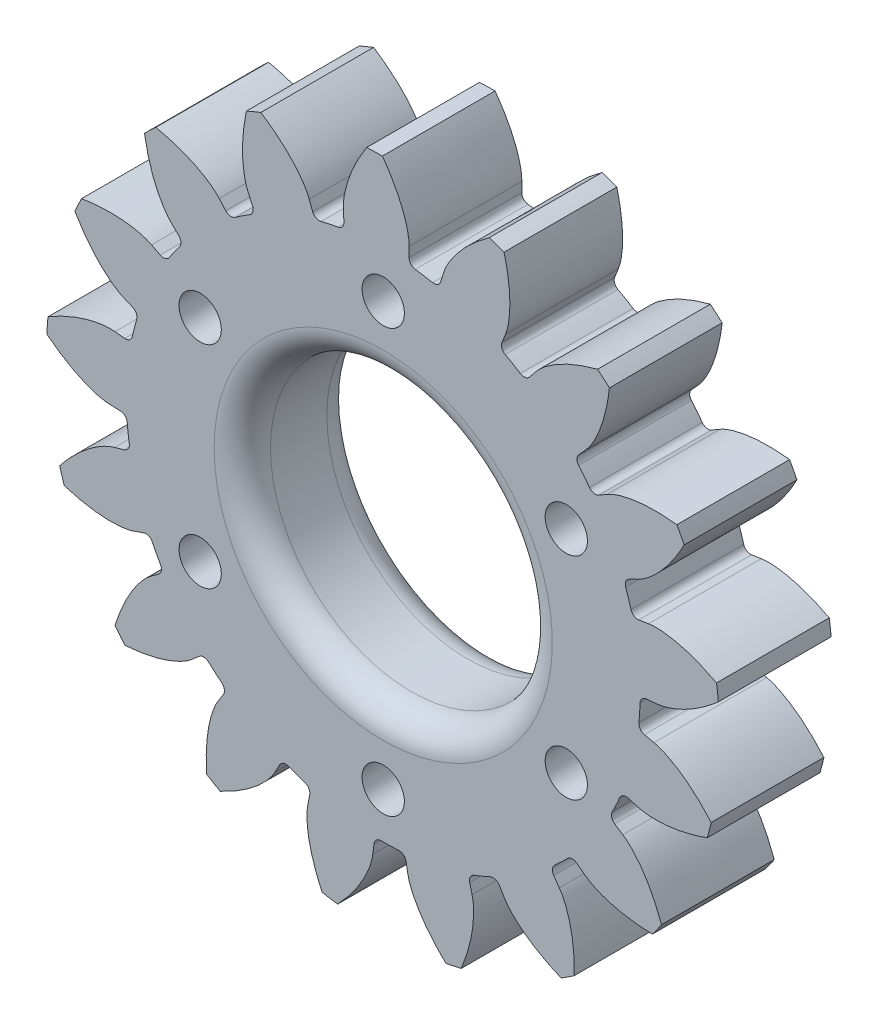
SolidWorks part; units mm, degrees
ref_plane "Front" through (0, 0, 0) normal (0, 0, 1) x (1, 0, 0)
ref_plane "Top" through (0, 0, 0) normal (0, 1, 0) x (1, 0, 0)
ref_plane "Right" through (0, 0, 0) normal (1, 0, 0) x (0, 0, -1)
sketch "Sketch1" plane through (0, 0, 0) normal (0, 0, 1) x (1, 0, 0)
  line L68 (2.1427, 9.4464) -> (2.0368, 9.1165)
  line L69 (0.916, 9.2963) -> (0.9185, 9.6427)
  line L70 (-1.4144, 9.5825) -> (-1.394, 9.2367)
  line L71 (-2.504, 8.9994) -> (-2.6268, 9.3234)
  line L72 (-4.7805, 8.4245) -> (-4.6366, 8.1093)
  line L73 (-5.5859, 7.4871) -> (-5.8174, 7.7449)
  line L74 (-7.501, 6.1287) -> (-7.2529, 5.8868)
  line L75 (-7.9134, 4.9637) -> (-8.2224, 5.1204)
  line L76 (-9.2084, 3.0052) -> (-8.8897, 2.8692)
  line L77 (-9.1721, 1.7699) -> (-9.5168, 1.8043)
  line L78 (-9.6722, -0.5242) -> (-9.3259, -0.5358)
  line L79 (-9.1921, -1.663) -> (-9.526, -1.7554)
  line L80 (-8.8296, -3.9828) -> (-8.5026, -3.8686)
  line L81 (-7.9706, -4.8713) -> (-8.2486, -5.078)
  line L82 (-6.7946, -6.9035) -> (-6.5309, -6.6788)
  line L83 (-5.6727, -7.4216) -> (-5.8572, -7.7148)
  line L84 (-3.842, -8.8918) -> (-3.6772, -8.587)
  line L85 (-2.6086, -8.9696) -> (-2.6747, -9.3097)
  line L86 (-0.3704, -9.6793) -> (-0.3269, -9.3356)
  line L87 (0.8078, -9.3063) -> (0.8689, -9.6473)
  line L88 (3.1511, -9.1595) -> (3.0675, -8.8232)
  line L89 (4.115, -8.3861) -> (4.2953, -8.6819)
  line L90 (6.2471, -7.4026) -> (6.0477, -7.1193)
  line L91 (6.8665, -6.3332) -> (7.1415, -6.544)
  line L92 (8.4994, -4.646) -> (8.2111, -4.4539)
  line L93 (8.6907, -3.4251) -> (9.0232, -3.5223)
  line L94 (9.6038, -1.2619) -> (9.2656, -1.1869)
  line L95 (9.3411, -0.0544) -> (9.6863, -0.0249)
  line L96 (9.4111, 2.2926) -> (9.0686, 2.2404)
  line L97 (8.73, 3.3237) -> (9.0412, 3.4759)
  line L98 (7.9475, 5.5374) -> (7.6469, 5.365)
  line L99 (6.9398, 6.2529) -> (7.1751, 6.5072)
  line L100 (5.4104, 8.0345) -> (5.1925, 7.7651)
  line L101 (4.2123, 8.3376) -> (4.3399, 8.6597)
  circle A0 centre (0, 0) radius 5
  arc A136 (4.2867, 11.1494) -> (3.764, 11.3366) centre (0, 0) ccw
  arc A137 (1.7491, 8.9466) -> (2.0368, 9.1165) centre (1.7973, 9.1934) ccw
  arc A138 (1.7491, 8.9466) -> (1.1361, 9.0449) centre (0, 0) ccw
  arc A139 (0.916, 9.2963) -> (1.1361, 9.0449) centre (1.1675, 9.2944) ccw
  arc A140 (-0.0304, 11.945) -> (-0.5854, 11.9307) centre (0, 0) ccw
  arc A141 (-1.6009, 8.9743) -> (-1.394, 9.2367) centre (-1.6451, 9.2219) ccw
  arc A142 (-1.6009, 8.9743) -> (-2.208, 8.8445) centre (0, 0) ccw
  arc A143 (-2.504, 8.9994) -> (-2.208, 8.8445) centre (-2.2689, 9.0885) ccw
  arc A144 (-4.3434, 11.1274) -> (-4.8558, 10.9136) centre (0, 0) ccw
  arc A145 (-4.7347, 7.79) -> (-4.6366, 8.1093) centre (-4.8653, 8.0049) ccw
  arc A146 (-4.7347, 7.79) -> (-5.2539, 7.4497) centre (0, 0) ccw
  arc A147 (-5.5859, 7.4871) -> (-5.2539, 7.4497) centre (-5.3988, 7.6552) ccw
  arc A148 (-8.0698, 8.807) -> (-8.4703, 8.4225) centre (0, 0) ccw
  arc A149 (-7.229, 5.5536) -> (-7.2529, 5.8868) centre (-7.4285, 5.7068) ccw
  arc A150 (-7.229, 5.5536) -> (-7.5902, 5.0487) centre (0, 0) ccw
  arc A151 (-7.9134, 4.9637) -> (-7.5902, 5.0487) centre (-7.7996, 5.188) ccw
  arc A152 (-10.7063, 5.2971) -> (-10.9409, 4.7939) centre (0, 0) ccw
  arc A153 (-8.7471, 2.5671) -> (-8.8897, 2.8692) centre (-8.9884, 2.6379) ccw
  arc A154 (-8.7471, 2.5671) -> (-8.9015, 1.9659) centre (0, 0) ccw
  arc A155 (-9.1721, 1.7699) -> (-8.9015, 1.9659) centre (-9.147, 2.0201) ccw
  arc A156 (-11.8969, 1.0719) -> (-11.9338, 0.5179) centre (0, 0) ccw
  arc A157 (-9.0837, -0.766) -> (-9.3259, -0.5358) centre (-9.3343, -0.7872) ccw
  arc A158 (-9.0837, -0.766) -> (-9.0105, -1.3825) centre (0, 0) ccw
  arc A159 (-9.1921, -1.663) -> (-9.0105, -1.3825) centre (-9.2591, -1.4206) ccw
  arc A160 (-11.4807, -3.2982) -> (-11.3151, -3.8281) centre (0, 0) ccw
  arc A161 (-8.1936, -3.9957) -> (-8.5026, -3.8686) centre (-8.4196, -4.106) ccw
  arc A162 (-8.1936, -3.9957) -> (-7.9027, -4.5441) centre (0, 0) ccw
  arc A163 (-7.9706, -4.8713) -> (-7.9027, -4.5441) centre (-8.1207, -4.6695) ccw
  arc A164 (-9.514, -7.2228) -> (-9.1681, -7.6571) centre (0, 0) ccw
  arc A165 (-6.1969, -6.6858) -> (-6.5309, -6.6788) centre (-6.3678, -6.8702) ccw
  arc A166 (-6.1969, -6.6858) -> (-5.7275, -7.092) centre (0, 0) ccw
  arc A167 (-5.6727, -7.4216) -> (-5.7275, -7.092) centre (-5.8855, -7.2877) ccw
  arc A168 (-6.2624, -10.1719) -> (-5.783, -10.4519) centre (0, 0) ccw
  arc A169 (-3.3632, -8.4729) -> (-3.6772, -8.587) centre (-3.456, -8.7066) ccw
  arc A170 (-3.3632, -8.4729) -> (-2.7788, -8.6821) centre (0, 0) ccw
  arc A171 (-2.6086, -8.9696) -> (-2.7788, -8.6821) centre (-2.8554, -8.9216) ccw
  arc A172 (-2.165, -11.7472) -> (-1.6168, -11.8352) centre (0, 0) ccw
  arc A173 (-0.0754, -9.1157) -> (-0.3269, -9.3356) centre (-0.0774, -9.3671) ccw
  arc A174 (-0.0754, -9.1157) -> (0.5452, -9.0997) centre (0, 0) ccw
  arc A175 (0.8078, -9.3063) -> (0.5452, -9.0997) centre (0.5602, -9.3507) ccw
  arc A176 (2.2248, -11.7361) -> (2.7677, -11.62) centre (0, 0) ccw
  arc A177 (3.2227, -8.5273) -> (3.0675, -8.8232) centre (3.3116, -8.7626) ccw
  arc A178 (3.2227, -8.5273) -> (3.7956, -8.2882) centre (0, 0) ccw
  arc A179 (4.115, -8.3861) -> (3.7956, -8.2882) centre (3.9003, -8.5169) ccw
  arc A180 (6.3141, -10.1399) -> (6.7785, -9.8355) centre (0, 0) ccw
  arc A181 (6.0855, -6.7873) -> (6.0477, -7.1193) centre (6.2534, -6.9746) ccw
  arc A182 (6.0855, -6.7873) -> (6.5333, -6.3574) centre (0, 0) ccw
  arc A183 (6.8665, -6.3332) -> (6.5333, -6.3574) centre (6.7135, -6.5328) ccw
  arc A184 (9.5507, -7.1742) -> (9.8737, -6.7227) centre (0, 0) ccw
  arc A185 (8.1264, -4.1307) -> (8.2111, -4.4539) centre (8.3506, -4.2446) ccw
  arc A186 (8.1264, -4.1307) -> (8.3887, -3.568) centre (0, 0) ccw
  arc A187 (8.6907, -3.4251) -> (8.3887, -3.568) centre (8.6201, -3.6665) ccw
  arc A188 (11.4974, -3.2397) -> (11.6355, -2.7019) centre (0, 0) ccw
  arc A189 (9.0698, -0.9161) -> (9.2656, -1.1869) centre (9.32, -0.9414) ccw
  arc A190 (9.0698, -0.9161) -> (9.1112, -0.2967) centre (0, 0) ccw
  arc A191 (9.3411, -0.0544) -> (9.1112, -0.2967) centre (9.3625, -0.3049) ccw
  arc A192 (11.8913, 1.1324) -> (11.8258, 1.6838) centre (0, 0) ccw
  arc A193 (8.7883, 2.4221) -> (9.0686, 2.2404) centre (9.0307, 2.489) ccw
  arc A194 (8.7883, 2.4221) -> (8.6031, 3.0146) centre (0, 0) ccw
  arc A195 (8.73, 3.3237) -> (8.6031, 3.0146) centre (8.8404, 3.0978) ccw
  arc A196 (10.6792, 5.3516) -> (10.419, 5.842) centre (0, 0) ccw
  arc A197 (7.3199, 5.4333) -> (7.6469, 5.365) centre (7.5218, 5.5832) ccw
  arc A198 (7.3199, 5.4333) -> (6.9331, 5.9189) centre (0, 0) ccw
  arc A199 (6.9398, 6.2529) -> (6.9331, 5.9189) centre (7.1244, 6.0821) ccw
  arc A200 (8.0248, 8.848) -> (7.605, 9.2113) centre (0, 0) ccw
  arc A201 (4.8629, 7.7106) -> (5.1925, 7.7651) centre (4.997, 7.9233) ccw
  arc A202 (4.8629, 7.7106) -> (4.3268, 8.0237) centre (0, 0) ccw
  arc A203 (4.2123, 8.3376) -> (4.3268, 8.0237) centre (4.4462, 8.245) ccw
  spline S68 degree 3 poles (3.764, 11.3366) (3.2587, 10.9714) (2.6231, 10.3935) (2.2067, 9.6531) (2.1427, 9.4464) knots -0.008485 -0.008485 -0.008485 -0.008485 0.741457 1 1 1 1
  spline S69 degree 3 poles (0.9185, 9.6427) (0.9201, 9.8535) (0.7567, 10.6863) (0.3366, 11.435) (-0.0304, 11.945) knots 0 0 0 0 0.250058 1 1 1 1
  spline S70 degree 3 poles (-0.5854, 11.9307) (-0.9247, 11.4077) (-1.3085, 10.6392) (-1.4294, 9.7984) (-1.4144, 9.5825) knots -0.008485 -0.008485 -0.008485 -0.008485 0.741457 1 1 1 1
  spline S71 degree 3 poles (-2.6268, 9.3234) (-2.7015, 9.5204) (-3.1547, 10.238) (-3.8169, 10.7844) (-4.3434, 11.1274) knots 0 0 0 0 0.250058 1 1 1 1
  spline S72 degree 3 poles (-4.8558, 10.9136) (-4.9832, 10.3033) (-5.0635, 9.4481) (-4.8725, 8.6204) (-4.7805, 8.4245) knots -0.008485 -0.008485 -0.008485 -0.008485 0.741457 1 1 1 1
  spline S73 degree 3 poles (-5.8174, 7.7449) (-5.9583, 7.9016) (-6.64, 8.4071) (-7.455, 8.6773) (-8.0698, 8.807) knots 0 0 0 0 0.250058 1 1 1 1
  spline S74 degree 3 poles (-8.4703, 8.4225) (-8.3687, 7.8074) (-8.1346, 6.9809) (-7.6575, 6.2781) (-7.501, 6.1287) knots -0.008485 -0.008485 -0.008485 -0.008485 0.741457 1 1 1 1
  spline S75 degree 3 poles (-8.2224, 5.1204) (-8.4103, 5.2157) (-9.2286, 5.4407) (-10.0862, 5.3983) (-10.7063, 5.2971) knots 0 0 0 0 0.250058 1 1 1 1
  spline S76 degree 3 poles (-10.9409, 4.7939) (-10.624, 4.2571) (-10.1071, 3.5709) (-9.4083, 3.088) (-9.2084, 3.0052) knots -0.008485 -0.008485 -0.008485 -0.008485 0.741457 1 1 1 1
  spline S77 degree 3 poles (-9.5168, 1.8043) (-9.7265, 1.8253) (-10.5708, 1.7395) (-11.3552, 1.3902) (-11.8969, 1.0719) knots 0 0 0 0 0.250058 1 1 1 1
  spline S78 degree 3 poles (-11.9338, 0.5179) (-11.4444, 0.1318) (-10.7145, -0.3213) (-9.8885, -0.5192) (-9.6722, -0.5242) knots -0.008485 -0.008485 -0.008485 -0.008485 0.741457 1 1 1 1
  spline S79 degree 3 poles (-9.526, -1.7554) (-9.7291, -1.8116) (-10.4854, -2.1966) (-11.0906, -2.8056) (-11.4807, -3.2982) knots 0 0 0 0 0.250058 1 1 1 1
  spline S80 degree 3 poles (-11.3151, -3.8281) (-10.7192, -4.0113) (-9.875, -4.1701) (-9.0332, -4.0563) (-8.8296, -3.9828) knots -0.008485 -0.008485 -0.008485 -0.008485 0.741457 1 1 1 1
  spline S81 degree 3 poles (-8.2486, -5.078) (-8.4177, -5.2038) (-8.9839, -5.836) (-9.3281, -6.6225) (-9.514, -7.2228) knots 0 0 0 0 0.250058 1 1 1 1
  spline S82 degree 3 poles (-9.1681, -7.6571) (-8.5463, -7.6126) (-7.7017, -7.4558) (-6.9579, -7.0456) (-6.7946, -6.9035) knots -0.008485 -0.008485 -0.008485 -0.008485 0.741457 1 1 1 1
  spline S83 degree 3 poles (-5.8572, -7.7148) (-5.9694, -7.8932) (-6.269, -8.6873) (-6.3059, -9.545) (-6.2624, -10.1719) knots 0 0 0 0 0.250058 1 1 1 1
  spline S84 degree 3 poles (-5.783, -10.4519) (-5.2192, -10.1859) (-4.4883, -9.7345) (-3.9429, -9.0833) (-3.842, -8.8918) knots -0.008485 -0.008485 -0.008485 -0.008485 0.741457 1 1 1 1
  spline S85 degree 3 poles (-2.6747, -9.3097) (-2.715, -9.5166) (-2.7074, -10.3653) (-2.432, -11.1784) (-2.165, -11.7472) knots 0 0 0 0 0.250058 1 1 1 1
  spline S86 degree 3 poles (-1.6168, -11.8352) (-1.1872, -11.3834) (-0.6687, -10.6985) (-0.3954, -9.8942) (-0.3704, -9.6793) knots -0.008485 -0.008485 -0.008485 -0.008485 0.741457 1 1 1 1
  spline S87 degree 3 poles (0.8689, -9.6473) (0.9062, -9.8547) (1.2197, -10.6434) (1.7703, -11.3021) (2.2248, -11.7361) knots 0 0 0 0 0.250058 1 1 1 1
  spline S88 degree 3 poles (2.7677, -11.62) (3.0051, -11.0436) (3.2412, -10.2176) (3.2055, -9.3689) (3.1511, -9.1595) knots -0.008485 -0.008485 -0.008485 -0.008485 0.741457 1 1 1 1
  spline S89 degree 3 poles (4.2953, -8.6819) (4.4049, -8.8619) (4.9822, -9.484) (5.7336, -9.8994) (6.3141, -10.1399) knots 0 0 0 0 0.250058 1 1 1 1
  spline S90 degree 3 poles (6.7785, -9.8355) (6.7916, -9.2122) (6.7134, -8.3568) (6.3735, -7.5783) (6.2471, -7.4026) knots -0.008485 -0.008485 -0.008485 -0.008485 0.741457 1 1 1 1
  spline S91 degree 3 poles (7.1415, -6.544) (7.3088, -6.6723) (8.0718, -7.0438) (8.9225, -7.1597) (9.5507, -7.1742) knots 0 0 0 0 0.250058 1 1 1 1
  spline S92 degree 3 poles (9.8737, -6.7227) (9.6608, -6.1367) (9.2788, -5.3673) (8.6807, -4.7642) (8.4994, -4.646) knots -0.008485 -0.008485 -0.008485 -0.008485 0.741457 1 1 1 1
  spline S93 degree 3 poles (9.0232, -3.5223) (9.2255, -3.5815) (10.0712, -3.6523) (10.9064, -3.4531) (11.4974, -3.2397) knots 0 0 0 0 0.250058 1 1 1 1
  spline S94 degree 3 poles (11.6355, -2.7019) (11.2253, -2.2324) (10.5911, -1.653) (9.8155, -1.3066) (9.6038, -1.2619) knots -0.008485 -0.008485 -0.008485 -0.008485 0.741457 1 1 1 1
  spline S95 degree 3 poles (9.6863, -0.0249) (9.8963, -0.007) (10.7105, 0.2325) (11.4173, 0.7199) (11.8913, 1.1324) knots 0 0 0 0 0.250058 1 1 1 1
  spline S96 degree 3 poles (11.8258, 1.6838) (11.2737, 1.9734) (10.4731, 2.2846) (9.6247, 2.3274) (9.4111, 2.2926) knots -0.008485 -0.008485 -0.008485 -0.008485 0.741457 1 1 1 1
  spline S97 degree 3 poles (9.0412, 3.4759) (9.2306, 3.5684) (9.9033, 4.0859) (10.3862, 4.7957) (10.6792, 5.3516) knots 0 0 0 0 0.250058 1 1 1 1
  spline S98 degree 3 poles (10.419, 5.842) (9.7996, 5.9126) (8.9406, 5.9136) (8.134, 5.6471) (7.9475, 5.5374) knots -0.008485 -0.008485 -0.008485 -0.008485 0.741457 1 1 1 1
  spline S99 degree 3 poles (7.1751, 6.5072) (7.3182, 6.6619) (7.7585, 7.3874) (7.9524, 8.2238) (8.0248, 8.848) knots 0 0 0 0 0.250058 1 1 1 1
  spline S100 degree 3 poles (7.605, 9.2113) (7.002, 9.0534) (6.2006, 8.744) (5.5448, 8.2041) (5.4104, 8.0345) knots -0.008485 -0.008485 -0.008485 -0.008485 0.741457 1 1 1 1
  spline S101 degree 3 poles (4.3399, 8.6597) (4.4174, 8.8557) (4.566, 9.6913) (4.4446, 10.5412) (4.2867, 11.1494) knots 0 0 0 0 0.250058 1 1 1 1
  dimension "D1" = 10
extrude "Boss-Extrude1" add sketch "Sketch1" along normal blind 4
sketch "Sketch3" plane through (0, 0, 4) normal (0, 0, 1) x (1, 0, 0)
  line L0 (0, 0) -> (-24.6444, 0)
sketch "Sketch4" plane through (0, 0, 4) normal (0, 0, 1) x (1, 0, 0)
  circle A0 centre (0, 0) radius 7.5 construction
  circle A1 centre (0, 7.5) radius 0.75
  circle A2 centre (6.4952, 3.75) radius 0.75
  circle A3 centre (6.4952, -3.75) radius 0.75
  circle A4 centre (0, -7.5) radius 0.75
  circle A5 centre (-6.4952, -3.75) radius 0.75
  circle A6 centre (-6.4952, 3.75) radius 0.75
  point P17 (0, 0)
  dimension "D1" = 1.5
  dimension "D2" = 15
  dimension "D3" = 6
extrude "Cut-Extrude1" cut sketch "Sketch4" against normal through all
fillet "Fillet1" radius 1 1 edges at (5, 0, 4)
fillet "Fillet2" radius 1 1 edges at (5, 0, 0)
